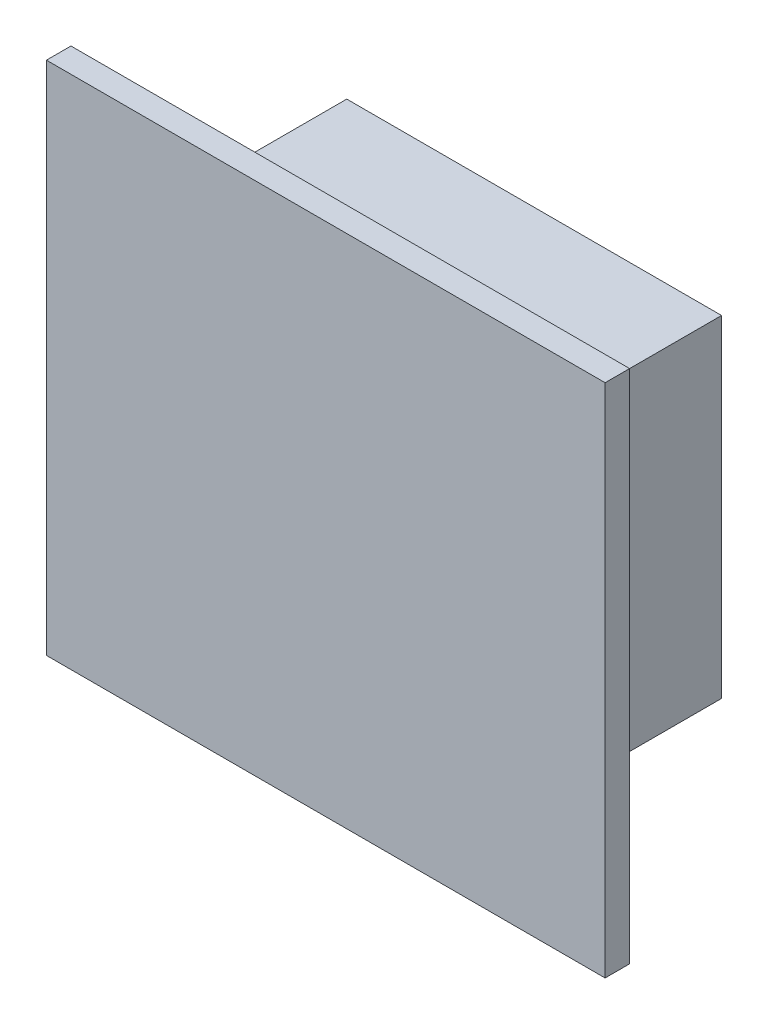
SolidWorks part; units mm, degrees
ref_plane "Front Plane" through (0, 0, 0) normal (0, 0, 1) x (1, 0, 0)
ref_plane "Top Plane" through (0, 0, 0) normal (0, 1, 0) x (1, 0, 0)
ref_plane "Right Plane" through (0, 0, 0) normal (1, 0, 0) x (0, 0, -1)
sketch "Sketch1" plane through (0, 0, 0) normal (0, 0, 1) x (1, 0, 0)
  line L0 (39.9241, -47.3232) -> (39.9241, -40.9117) construction
  line L1 (48.0393, -39.9117) -> (38.9241, -39.9117)
  line L2 (48.0393, -39.9117) -> (48.0393, -48.3232)
  line L3 (48.0393, -48.3232) -> (38.9241, -48.3232)
  line L4 (38.9241, -39.9117) -> (38.9241, -48.3232)
  line L5 (39.9241, -40.9117) -> (47.0393, -40.9117) construction
  line L6 (47.0393, -40.9117) -> (47.0393, -47.3232) construction
  line L7 (47.0393, -47.3232) -> (39.9241, -47.3232) construction
  dimension "D1" = 1
  dimension "D2" = 1
  dimension "D3" = 1
  dimension "D4" = 1
extrude "Boss-Extrude1" add sketch "Sketch1" along normal up to surface (0.4 mm away)
sketch "Sketch2" plane through (0, 0, 0) normal (0, 0, -1) x (-1, 0, 0)
  line L0 (-47.0393, -47.3232) -> (-39.9241, -47.3232) construction
  line L1 (-40.4241, -41.4117) -> (-46.5393, -41.4117)
  line L2 (-40.4241, -41.4117) -> (-40.4241, -46.8232)
  line L3 (-40.4241, -46.8232) -> (-46.5393, -46.8232)
  line L4 (-46.5393, -41.4117) -> (-46.5393, -46.8232)
  line L5 (-39.9241, -40.9117) -> (-47.0393, -40.9117) construction
  line L6 (-47.0393, -40.9117) -> (-47.0393, -47.3232) construction
  line L7 (-39.9241, -47.3232) -> (-39.9241, -40.9117) construction
  dimension "D1" = 0.5
  dimension "D2" = 0.5
  dimension "D3" = 0.5
  dimension "D4" = 0.5
extrude "Boss-Extrude2" add sketch "Sketch2" along normal blind 3
